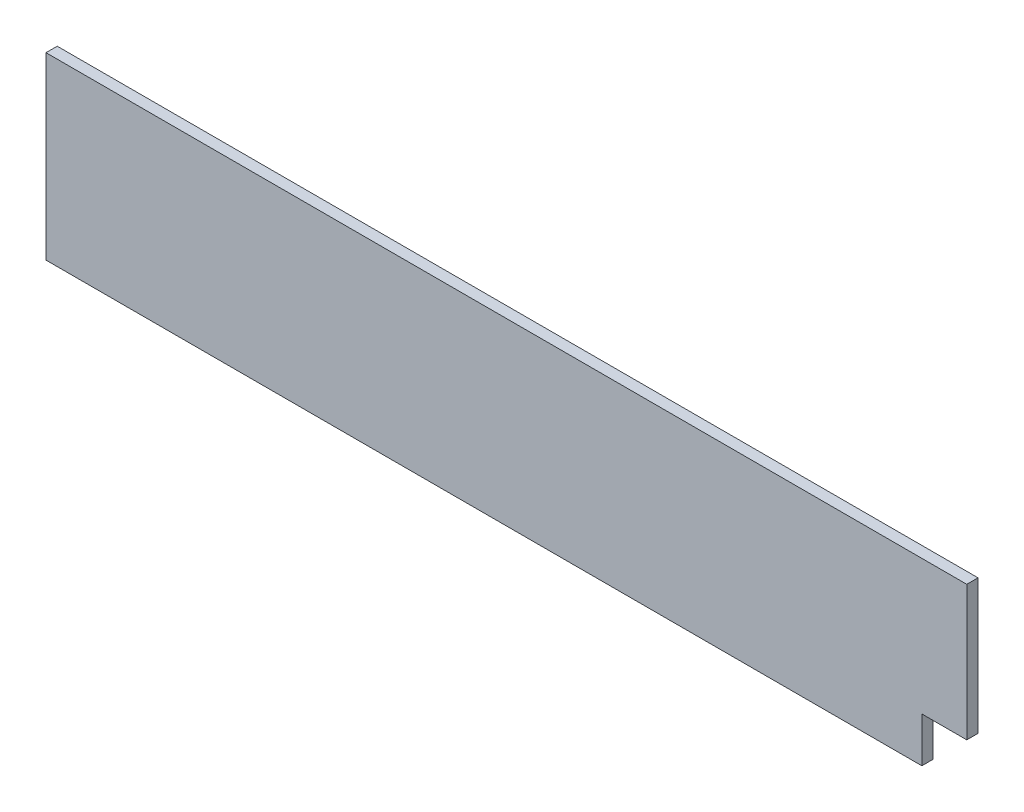
SolidWorks part; units mm, degrees
ref_plane "Plano frontal" through (0, 0, 0) normal (0, 0, 1) x (1, 0, 0)
ref_plane "Plano superior" through (0, 0, 0) normal (0, 1, 0) x (1, 0, 0)
ref_plane "Plano direito" through (0, 0, 0) normal (1, 0, 0) x (0, 0, -1)
sketch "Esboço1" plane through (0, 0, 0) normal (0, 0, 1) x (1, 0, 0)
  line L1 (0, 0) -> (2050, 0)
  line L2 (0, 0) -> (0, 400)
  line L3 (0, 400) -> (2050, 400)
  line L4 (2050, 0) -> (2050, 400)
  dimension "D1" = 2050
  dimension "D2" = 400
extrude "Ressalto-extrusão1" add sketch "Esboço1" along normal blind 25
sketch "Esboço3" plane through (0, 0, 25) normal (0, 0, 1) x (1, 0, 0)
  line L1 (2050, 0) -> (1950, 0)
  line L2 (2050, 0) -> (2050, 100)
  line L3 (2050, 100) -> (1950, 100)
  line L4 (1950, 0) -> (1950, 100)
  dimension "D1" = 100
  dimension "D2" = 100
extrude "Corte-extrusão2" cut sketch "Esboço3" against normal blind 25
